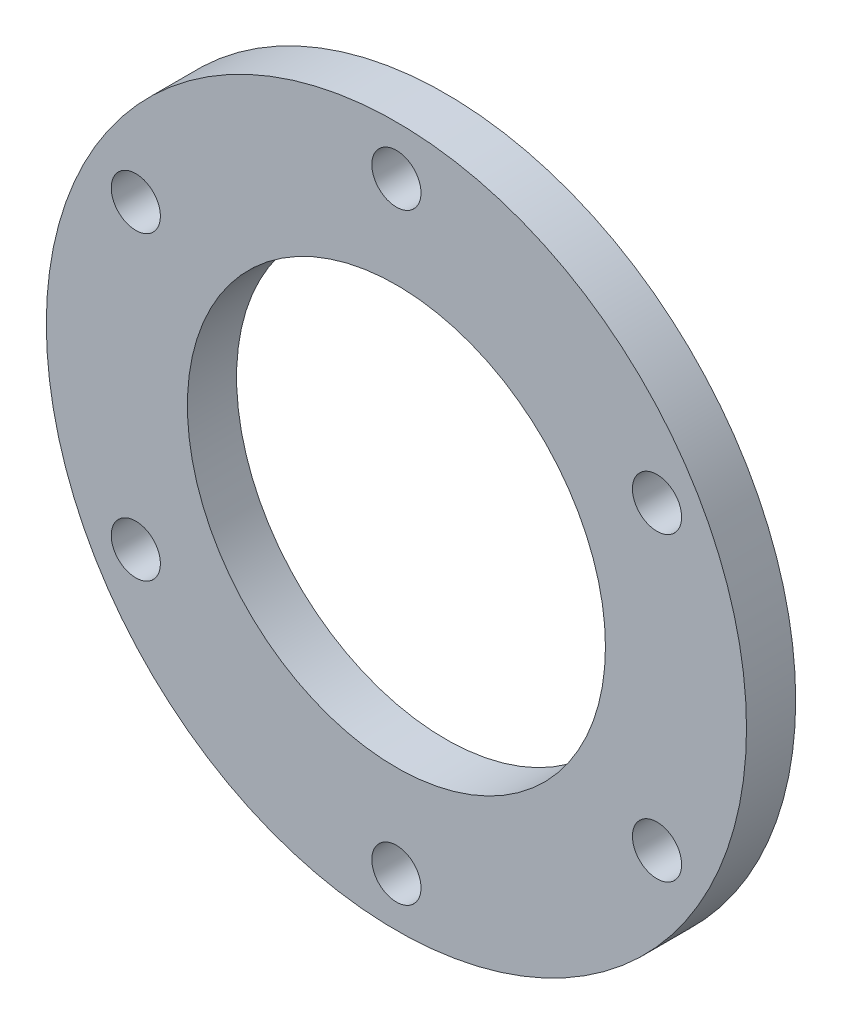
SolidWorks part; units mm, degrees
material "ABS"
ref_plane "Front Plane" through (0, 0, 0) normal (0, 0, 1) x (1, 0, 0)
ref_plane "Top Plane" through (0, 0, 0) normal (0, 1, 0) x (1, 0, 0)
ref_plane "Right Plane" through (0, 0, 0) normal (1, 0, 0) x (0, 0, -1)
sketch "Sketch1" plane through (0, 0, 0) normal (0, 0, 1) x (1, 0, 0)
  circle A0 centre (0, 0) radius 26.9875
  circle A1 centre (0, 0) radius 45.2
  circle A2 centre (0, 0) radius 38.85 construction
  circle A3 centre (0, 38.85) radius 3.175
  circle A4 centre (33.6451, 19.425) radius 3.175
  circle A5 centre (33.6451, -19.425) radius 3.175
  circle A6 centre (0, -38.85) radius 3.175
  circle A7 centre (-33.6451, -19.425) radius 3.175
  circle A8 centre (-33.6451, 19.425) radius 3.175
  point P20 (0, 0)
  dimension "D1" = 53.975
  dimension "D3" = 77.7
  dimension "D2" = 90.4
  dimension "D4" = 6.35
  dimension "D5" = 6
extrude "Boss-Extrude1" add sketch "Sketch1" along normal blind 6.35
